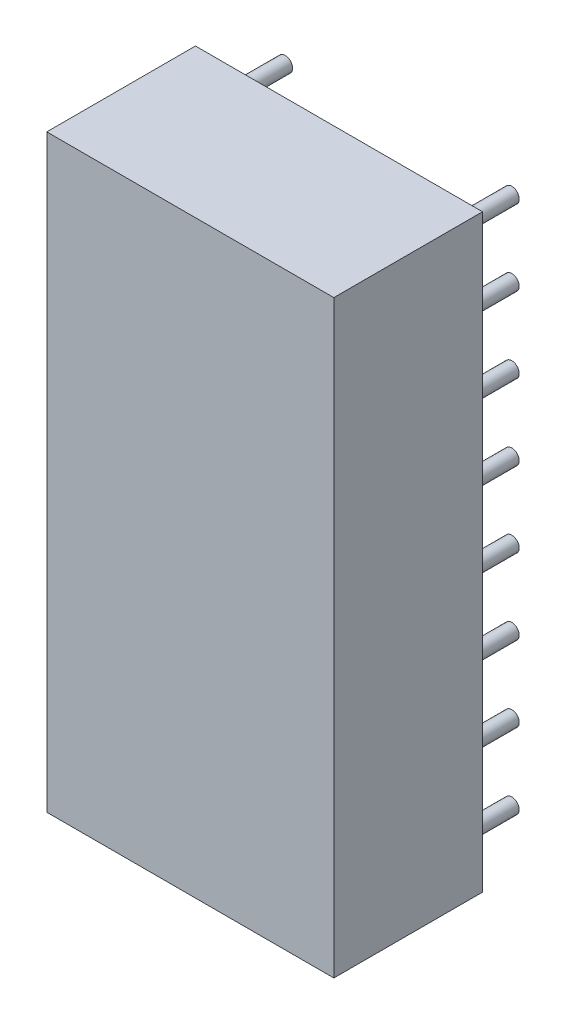
SolidWorks part; units mm, degrees
ref_plane "Front Plane" through (0, 0, 0) normal (0, 0, 1) x (1, 0, 0)
ref_plane "Top Plane" through (0, 0, 0) normal (0, 1, 0) x (1, 0, 0)
ref_plane "Right Plane" through (0, 0, 0) normal (1, 0, 0) x (0, 0, -1)
sketch "Sketch1" plane through (0, 0, 0) normal (0, 0, 1) x (1, 0, 0)
  line L0 (0.254, 0.254) -> (9.906, 0.254)
  line L1 (9.906, 0.254) -> (9.906, 20.066)
  line L2 (9.906, 20.066) -> (0.254, 20.066)
  line L3 (0.254, 20.066) -> (0.254, 0.254)
extrude "Component_Outline" add sketch "Sketch1" along normal blind 5 separate body
sketch "Sketch2" plane through (0, 0, 0) normal (0, 0, 1) x (1, 0, 0)
  circle A0 centre (1.27, 1.27) radius 0.25
extrude "1" add sketch "Sketch2" against normal blind 2 separate body
sketch "Sketch3" plane through (0, 0, 0) normal (0, 0, 1) x (1, 0, 0)
  circle A0 centre (1.27, 3.81) radius 0.25
extrude "2" add sketch "Sketch3" against normal blind 2 separate body
sketch "Sketch4" plane through (0, 0, 0) normal (0, 0, 1) x (1, 0, 0)
  circle A0 centre (1.27, 6.35) radius 0.25
extrude "3" add sketch "Sketch4" against normal blind 2 separate body
sketch "Sketch5" plane through (0, 0, 0) normal (0, 0, 1) x (1, 0, 0)
  circle A0 centre (1.27, 8.89) radius 0.25
extrude "4" add sketch "Sketch5" against normal blind 2 separate body
sketch "Sketch6" plane through (0, 0, 0) normal (0, 0, 1) x (1, 0, 0)
  circle A0 centre (1.27, 11.43) radius 0.25
extrude "5" add sketch "Sketch6" against normal blind 2 separate body
sketch "Sketch7" plane through (0, 0, 0) normal (0, 0, 1) x (1, 0, 0)
  circle A0 centre (1.27, 13.97) radius 0.25
extrude "6" add sketch "Sketch7" against normal blind 2 separate body
sketch "Sketch8" plane through (0, 0, 0) normal (0, 0, 1) x (1, 0, 0)
  circle A0 centre (1.27, 16.51) radius 0.25
extrude "7" add sketch "Sketch8" against normal blind 2 separate body
sketch "Sketch9" plane through (0, 0, 0) normal (0, 0, 1) x (1, 0, 0)
  circle A0 centre (1.27, 19.05) radius 0.25
extrude "8" add sketch "Sketch9" against normal blind 2 separate body
sketch "Sketch10" plane through (0, 0, 0) normal (0, 0, 1) x (1, 0, 0)
  circle A0 centre (8.89, 1.27) radius 0.25
extrude "9" add sketch "Sketch10" against normal blind 2 separate body
sketch "Sketch11" plane through (0, 0, 0) normal (0, 0, 1) x (1, 0, 0)
  circle A0 centre (8.89, 3.81) radius 0.25
extrude "10" add sketch "Sketch11" against normal blind 2 separate body
sketch "Sketch12" plane through (0, 0, 0) normal (0, 0, 1) x (1, 0, 0)
  circle A0 centre (8.89, 6.35) radius 0.25
extrude "11" add sketch "Sketch12" against normal blind 2 separate body
sketch "Sketch13" plane through (0, 0, 0) normal (0, 0, 1) x (1, 0, 0)
  circle A0 centre (8.89, 8.89) radius 0.25
extrude "12" add sketch "Sketch13" against normal blind 2 separate body
sketch "Sketch14" plane through (0, 0, 0) normal (0, 0, 1) x (1, 0, 0)
  circle A0 centre (8.89, 11.43) radius 0.25
extrude "13" add sketch "Sketch14" against normal blind 2 separate body
sketch "Sketch15" plane through (0, 0, 0) normal (0, 0, 1) x (1, 0, 0)
  circle A0 centre (8.89, 13.97) radius 0.25
extrude "14" add sketch "Sketch15" against normal blind 2 separate body
sketch "Sketch16" plane through (0, 0, 0) normal (0, 0, 1) x (1, 0, 0)
  circle A0 centre (8.89, 16.51) radius 0.25
extrude "15" add sketch "Sketch16" against normal blind 2 separate body
sketch "Sketch17" plane through (0, 0, 0) normal (0, 0, 1) x (1, 0, 0)
  circle A0 centre (8.89, 19.05) radius 0.25
extrude "16" add sketch "Sketch17" against normal blind 2 separate body
sketch3d "3DSketch1"
  line L0 (0, 0, 0) -> (1, 0, 0)
  line L1 (0, 0, 0) -> (0, 1, 0)
  line L2 (0, 0, 0) -> (0, 0, 1)
  point P0 (0, 0, 0)
